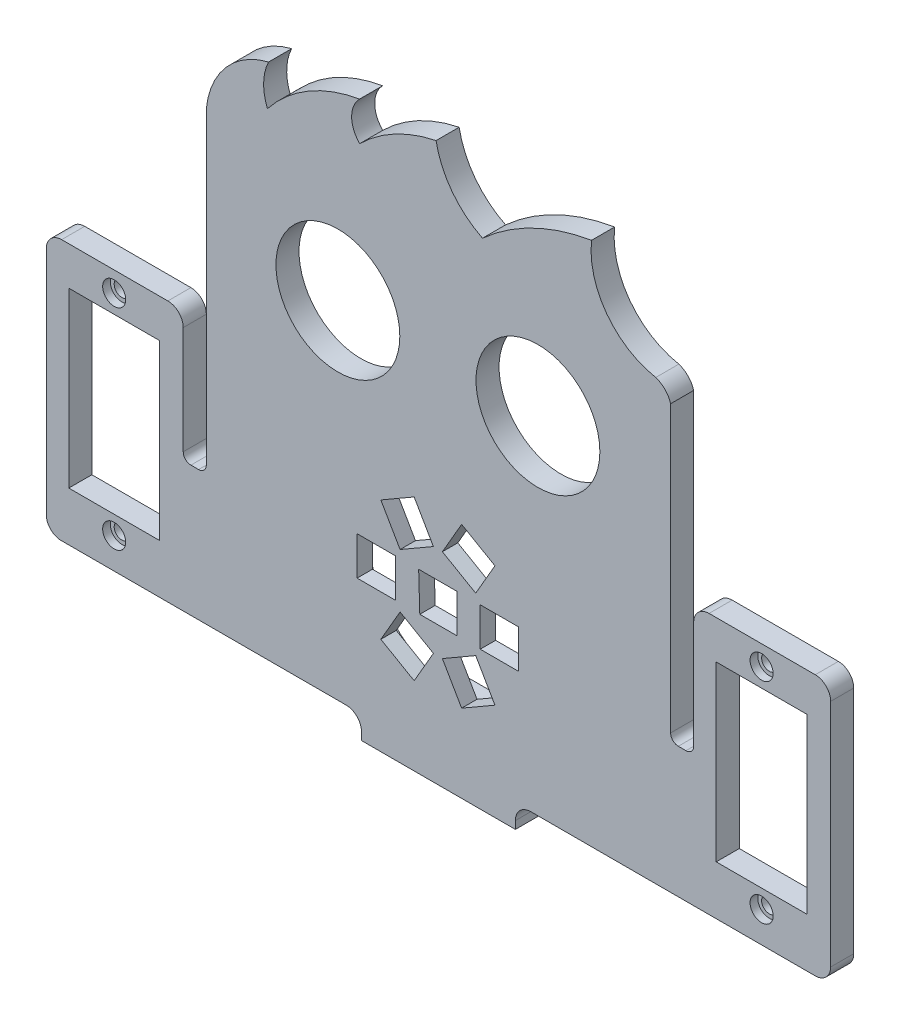
SolidWorks part; units mm, degrees
ref_plane "Alzado" through (0, 0, 0) normal (0, 0, 1) x (1, 0, 0)
ref_plane "Planta" through (0, 0, 0) normal (0, 1, 0) x (1, 0, 0)
ref_plane "Vista lateral" through (0, 0, 0) normal (1, 0, 0) x (0, 0, -1)
sketch "Model" plane through (0, 0, 0) normal (0, 0, 1) x (1, 0, 0)
  line L0 (53.2839, -43.3643) -> (57.614, -45.8643)
  line L1 (57.614, -45.8643) -> (60.114, -41.5341)
  line L2 (60.114, -41.5341) -> (55.7839, -39.0341)
  line L3 (55.7839, -39.0341) -> (53.2839, -43.3643)
  line L4 (63.7839, -45.8643) -> (68.114, -43.3643)
  line L5 (68.114, -43.3643) -> (65.614, -39.0341)
  line L6 (65.614, -39.0341) -> (61.2839, -41.5341)
  line L7 (61.2839, -41.5341) -> (63.7839, -45.8643)
  line L8 (71.199, -38.021) -> (71.199, -33.021)
  line L9 (71.199, -33.021) -> (66.199, -33.021)
  line L10 (66.199, -33.021) -> (66.199, -38.021)
  line L11 (66.199, -38.021) -> (71.199, -38.021)
  line L12 (68.114, -27.6777) -> (63.7839, -25.1777)
  line L13 (63.7839, -25.1777) -> (61.2839, -29.5079)
  line L14 (61.2839, -29.5079) -> (65.614, -32.0079)
  line L15 (65.614, -32.0079) -> (68.114, -27.6777)
  line L16 (57.614, -25.1777) -> (53.2839, -27.6777)
  line L17 (53.2839, -27.6777) -> (55.7839, -32.0079)
  line L18 (55.7839, -32.0079) -> (60.114, -29.5079)
  line L19 (60.114, -29.5079) -> (57.614, -25.1777)
  line L20 (50.199, -33.021) -> (50.199, -38.021)
  line L21 (50.199, -38.021) -> (55.199, -38.021)
  line L22 (55.199, -38.021) -> (55.199, -33.021)
  line L23 (55.199, -33.021) -> (50.199, -33.021)
  line L24 (58.199, -33.021) -> (58.3448, -38.021)
  line L25 (58.3448, -38.021) -> (63.199, -38.021)
  line L26 (63.199, -38.021) -> (63.199, -33.021)
  line L27 (63.199, -33.021) -> (58.199, -33.021)
  line L28 (28.6, -36.0989) -> (29.6, -36.0989)
  line L29 (92.9437, -36.071) -> (91.9437, -36.071)
  line L30 (27.6, -21.121) -> (27.6, -35.0989)
  line L31 (30.6, 4.9744) -> (30.6, -35.0989)
  line L32 (90.9437, 1.979) -> (90.9437, -35.071)
  line L33 (93.9437, -21.121) -> (93.9437, -35.071)
  line L34 (50.7719, -56.0206) -> (70.7719, -56.0206)
  line L35 (60.7719, -38.021) -> (60.7719, -56.0206) construction
  line L36 (11.7437, -53.0206) -> (48.7719, -53.0206)
  line L37 (109.7437, -53.021) -> (72.7719, -53.021)
  line L42 (96.8708, -46.621) -> (108.6708, -46.621)
  line L43 (108.6708, -46.621) -> (108.6708, -24.121)
  line L44 (108.6708, -24.121) -> (96.8708, -24.121)
  line L45 (96.8708, -24.121) -> (96.8708, -46.621)
  line L46 (12.7271, -24.121) -> (12.7271, -46.621)
  line L47 (12.7271, -46.621) -> (24.5271, -46.621)
  line L48 (24.5271, -46.621) -> (24.5271, -24.121)
  line L49 (24.5271, -24.121) -> (12.7271, -24.121)
  line L51 (50.7719, -55.0206) -> (50.7719, -56.0206)
  line L56 (70.7719, -56.0206) -> (70.7719, -55.021)
  line L61 (109.7437, -19.121) -> (95.9437, -19.121)
  line L62 (111.7437, -51.021) -> (111.7437, -21.121)
  line L96 (9.8, -21.121) -> (9.8, -51.0769)
  line L97 (25.6, -19.121) -> (11.8, -19.121)
  circle A0 centre (47.699, -8.021) radius 8.05
  circle A1 centre (73.699, -8.021) radius 8.05
  arc A2 (91.9437, -36.071) -> (90.9437, -35.071) centre (91.9437, -35.071) cw
  arc A3 (92.9437, -36.071) -> (93.9437, -35.071) centre (92.9437, -35.071) ccw
  arc A4 (29.6, -36.0989) -> (30.6, -35.0989) centre (29.6, -35.0989) ccw
  arc A5 (28.6, -36.0989) -> (27.6, -35.0989) centre (28.6, -35.0989) cw
  arc A6 (50.7719, -55.0206) -> (48.7719, -53.0206) centre (48.7719, -55.0206) ccw
  arc A7 (70.7719, -55.021) -> (72.7719, -53.021) centre (72.7719, -55.021) cw
  circle A10 centre (102.7708, -49.021) radius 1
  circle A11 centre (102.7708, -21.721) radius 1
  circle A12 centre (18.6271, -49.021) radius 1
  circle A13 centre (18.6271, -21.721) radius 1
  arc A36 (38.6912, 14.3189) -> (30.6, 4.9744) centre (41.1976, 3.9735) ccw
  arc A37 (38.6912, 14.3189) -> (38.5441, 8.9961) centre (44.5661, 11.4932) ccw
  arc A38 (50.5117, 16.0514) -> (38.5441, 8.9961) centre (53.6998, -3.0341) ccw
  arc A39 (50.5117, 16.0514) -> (50.5348, 11.0514) centre (53.0232, 13.5629) ccw
  arc A40 (60.4603, 16.3614) -> (50.5348, 11.0514) centre (64.4529, -3.0332) ccw
  arc A41 (60.4603, 16.3614) -> (66.4972, 8.3891) centre (71.451, 18.4121) ccw
  arc A42 (80.6653, 15.2365) -> (66.4972, 8.3891) centre (85.2429, -12.3168) ccw
  arc A43 (80.6653, 15.2365) -> (89.0134, 3.9735) centre (90.9108, 14.1051) ccw
  arc A44 (90.9437, 1.979) -> (89.0134, 3.9735) centre (88.0674, 1.1265) ccw
  arc A47 (95.9437, -19.121) -> (93.9437, -21.121) centre (95.9437, -21.121) ccw
  arc A48 (111.7437, -21.121) -> (109.7437, -19.121) centre (109.7437, -21.121) ccw
  arc A49 (109.7437, -53.021) -> (111.7437, -51.021) centre (109.7437, -51.021) ccw
  arc A66 (9.8, -51.0769) -> (11.7437, -53.0206) centre (11.7437, -51.0769) ccw
  arc A67 (11.8, -19.121) -> (9.8, -21.121) centre (11.8, -21.121) ccw
  arc A68 (27.6, -21.121) -> (25.6, -19.121) centre (25.6, -21.121) ccw
  dimension "D1" = 1
  dimension "D2" = 2
extrude "Saliente-Extruir1" add sketch "Model" along normal blind 3
sketch "Croquis2" plane through (0, 0, 3) normal (0, 0, 1) x (1, 0, 0)
  circle A0 centre (18.6271, -21.721) radius 1.5
  circle A1 centre (18.6271, -49.021) radius 1.5
  circle A2 centre (102.7708, -49.021) radius 1.5
  circle A3 centre (102.7708, -21.721) radius 1.5
extrude "Cortar-Extruir1" cut sketch "Croquis2" against normal blind 1
sketch "Croquis4" plane through (0, 0, 0) normal (0, 0, -1) x (-1, 0, 0)
  line L0 (-70.7719, -56.0206) -> (-70.7719, -53.0206)
  line L1 (-70.7719, -53.0206) -> (-50.7719, -53.0206)
  line L2 (-50.7719, -53.0206) -> (-50.7719, -56.0206)
  line L19 (-91.9437, -36.071) -> (-92.9437, -36.071)
  line L20 (-93.9437, -35.071) -> (-93.9437, -21.121)
  line L21 (-95.9437, -19.121) -> (-109.7437, -19.121)
  line L22 (-111.7437, -21.121) -> (-111.7437, -51.021)
  line L23 (-109.7437, -53.021) -> (-72.7719, -53.021)
  line L24 (-70.7719, -55.021) -> (-70.7719, -56.0206)
  line L25 (-70.7719, -56.0206) -> (-50.7719, -56.0206)
  line L26 (-50.7719, -56.0206) -> (-50.7719, -55.0206)
  line L27 (-48.7719, -53.0206) -> (-11.7437, -53.0206)
  line L28 (-9.8, -51.0769) -> (-9.8, -21.121)
  line L29 (-11.8, -19.121) -> (-25.6, -19.121)
  line L30 (-27.6, -21.121) -> (-27.6, -35.0989)
  line L31 (-28.6, -36.0989) -> (-29.6, -36.0989)
  line L32 (-30.6, -35.0989) -> (-30.6, 4.9744)
  line L33 (-90.9437, 1.979) -> (-90.9437, -35.071)
  line L40 (-70.7719, -56.0206) -> (-50.7719, -56.0206)
  arc A21 (-91.9437, -36.071) -> (-90.9437, -35.071) centre (-91.9437, -35.071) ccw
  arc A22 (-93.9437, -35.071) -> (-92.9437, -36.071) centre (-92.9437, -35.071) ccw
  arc A23 (-93.9437, -21.121) -> (-95.9437, -19.121) centre (-95.9437, -21.121) ccw
  arc A24 (-109.7437, -19.121) -> (-111.7437, -21.121) centre (-109.7437, -21.121) ccw
  arc A25 (-111.7437, -51.021) -> (-109.7437, -53.021) centre (-109.7437, -51.021) ccw
  arc A26 (-70.7719, -55.021) -> (-72.7719, -53.021) centre (-72.7719, -55.021) ccw
  arc A27 (-48.7719, -53.0206) -> (-50.7719, -55.0206) centre (-48.7719, -55.0206) ccw
  arc A28 (-11.7437, -53.0206) -> (-9.8, -51.0769) centre (-11.7437, -51.0769) ccw
  arc A29 (-9.8, -21.121) -> (-11.8, -19.121) centre (-11.8, -21.121) ccw
  arc A30 (-25.6, -19.121) -> (-27.6, -21.121) centre (-25.6, -21.121) ccw
  arc A31 (-28.6, -36.0989) -> (-27.6, -35.0989) centre (-28.6, -35.0989) ccw
  arc A32 (-30.6, -35.0989) -> (-29.6, -36.0989) centre (-29.6, -35.0989) ccw
  arc A33 (-30.6, 4.9744) -> (-38.6912, 14.3189) centre (-41.1976, 3.9735) ccw
  arc A34 (-38.5441, 8.9961) -> (-38.6912, 14.3189) centre (-44.5661, 11.4932) ccw
  arc A35 (-38.5441, 8.9961) -> (-50.5117, 16.0514) centre (-53.6998, -3.0341) ccw
  arc A36 (-50.5348, 11.0514) -> (-50.5117, 16.0514) centre (-53.0232, 13.5629) ccw
  arc A37 (-50.5348, 11.0514) -> (-60.4603, 16.3614) centre (-64.4529, -3.0332) ccw
  arc A38 (-66.4972, 8.3891) -> (-60.4603, 16.3614) centre (-71.451, 18.4121) ccw
  arc A39 (-66.4972, 8.3891) -> (-80.6653, 15.2365) centre (-85.2429, -12.3168) ccw
  arc A40 (-89.0134, 3.9735) -> (-80.6653, 15.2365) centre (-90.9108, 14.1051) ccw
  arc A41 (-89.0134, 3.9735) -> (-90.9437, 1.979) centre (-88.0674, 1.1265) ccw
  dimension "D1" = 3
  dimension "D2" = 0
extrude "Saliente-Extruir2" add sketch "Croquis4" along normal blind 8
sketch "Croquis5" plane through (0, -53.0206, 0) normal (0, 1, 0) x (1, 0, 0)
  line L0 (60.7719, 8) -> (60.7719, 0) construction
  line L1 (50.7719, 8) -> (70.7719, 8) construction
  line L2 (50.7719, 0) -> (70.7719, 0) construction
  circle A0 centre (66.7719, 3.5) radius 1.5
  circle A1 centre (54.7719, 3.5) radius 1.5
  dimension "D1" = 6
  dimension "D2" = 3.5
extrude "Cortar-Extruir2" cut sketch "Croquis5" against normal blind 3
fillet "Redondeo1" radius 2 2 edges at (50.7719, -54.5206, -8) (70.7719, -54.5206, -8)
sketch "Croquis6" plane through (0, 0, 0) normal (0, 0, -1) x (-1, 0, 0)
  line L0 (-90.9437, -35.5206) -> (-30.6, -35.5206) construction
  line L6 (-11.7437, -53.0206) -> (-48.7719, -53.0206) construction
  circle A0 centre (-60.7719, -35.5206) radius 12
  dimension "D1" = 17.5
extrude "Cortar-Extruir3" cut sketch "Croquis6" against normal blind 1
